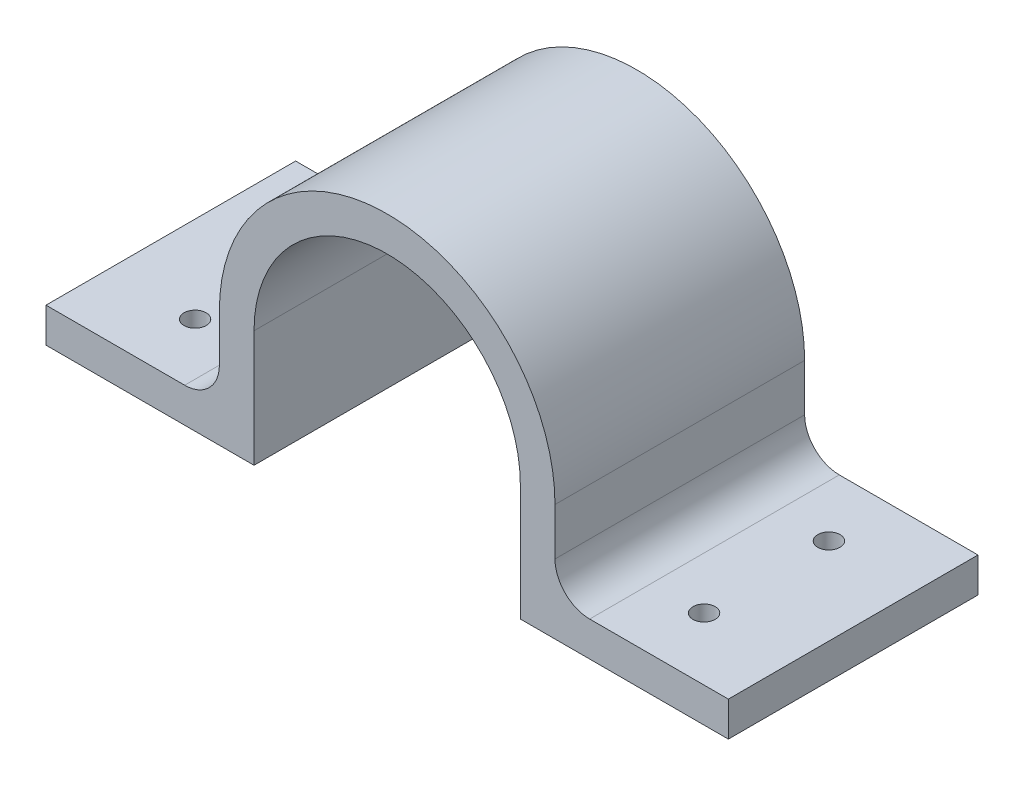
SolidWorks part; units mm, degrees
ref_plane "Front Plane" through (0, 0, 0) normal (0, 0, 1) x (1, 0, 0)
ref_plane "Top Plane" through (0, 0, 0) normal (0, 1, 0) x (1, 0, 0)
ref_plane "Right Plane" through (0, 0, 0) normal (1, 0, 0) x (0, 0, -1)
sketch "Sketch1" plane through (0, 0, 0) normal (0, 0, 1) x (1, 0, 0)
  line L0 (0, 19.2) -> (-33.9115, 19.2) construction
  line L1 (-19.2, 0) -> (-19.2, -16.8)
  line L2 (0, 19.2) -> (0, -19.299) construction
  line L3 (19.2, 0) -> (19.2, -16.8)
  line L4 (0, -19.299) -> (-19.2, -19.299) construction
  line L5 (-19.2, -16.8) -> (-49.2, -16.8)
  line L6 (19.2, -16.8) -> (49.2, -16.8)
  line L7 (24.2, -11.8) -> (49.2, -11.8)
  line L8 (24.2, 0) -> (24.2, -11.8)
  line L9 (-24.2, 0) -> (-24.2, -11.8)
  line L10 (-24.2, -11.8) -> (-49.2, -11.8)
  line L11 (-49.2, -11.8) -> (-49.2, -16.8)
  line L12 (49.2, -11.8) -> (49.2, -16.8)
  arc A0 (19.2, 0) -> (-19.2, 0) centre (0, 0) ccw
  arc A1 (24.2, 0) -> (-24.2, 0) centre (0, 0) ccw
  dimension "D1" = 30
  dimension "D3" = 38.4
  dimension "D4" = 36
  dimension "D2" = 5
extrude "Boss-Extrude1" add sketch "Sketch1" against normal blind 36
sketch "Sketch2" plane through (0, -11.8, 0) normal (0, 1, 0) x (1, 0, 0)
  line L0 (-36.7, 36) -> (-36.7, 0) construction
  line L1 (-24.2, 36) -> (-49.2, 36) construction
  line L2 (-24.2, 0) -> (-49.2, 0) construction
  line L3 (-49.2, 18) -> (-24.2, 18) construction
  line L4 (-49.2, 36) -> (-49.2, 0) construction
  line L5 (-24.2, 36) -> (-24.2, 0) construction
  line L6 (0, 36) -> (0, 0) construction
  line L7 (24.2, 36) -> (-24.2, 36) construction
  circle A0 centre (-36.7, 27) radius 1.6
  circle A1 centre (-36.7, 9) radius 1.6
  circle A2 centre (36.7, 27) radius 1.6
  circle A3 centre (36.7, 9) radius 1.6
  dimension "D1" = 9
extrude "Cut-Extrude1" cut sketch "Sketch2" against normal blind 5
fillet "Fillet1" radius 5 2 edges at (24.2, -11.8, -18) (-24.2, -11.8, -18)
